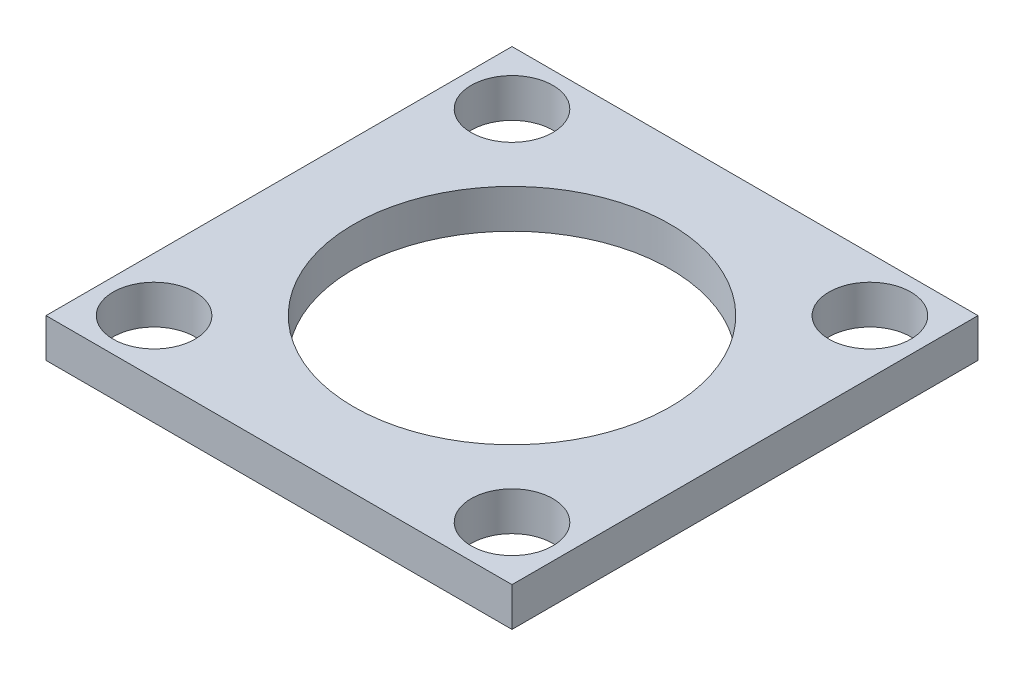
SolidWorks part; units mm, degrees
ref_plane "Plan de face" through (0, 0, 0) normal (0, 0, 1) x (1, 0, 0)
ref_plane "Plan de dessus" through (0, 0, 0) normal (0, 1, 0) x (1, 0, 0)
ref_plane "Plan de droite" through (0, 0, 0) normal (1, 0, 0) x (0, 0, -1)
sketch "Esquisse1" plane through (0, 0, 0) normal (0, 1, 0) x (1, 0, 0)
  line L1 (0, 0) -> (6, 0)
  line L2 (0, 0) -> (0, 6)
  line L3 (0, 6) -> (6, 6)
  line L4 (6, 0) -> (6, 6)
  dimension "D1" = 6
  dimension "D2" = 6
extrude "Extrusion1" add sketch "Esquisse1" along normal blind 0.5
sketch "Esquisse2" plane through (0, 0.5, 0) normal (0, 1, 0) x (-1, 0, 0)
  circle A0 centre (-3, -3) radius 2.0371
extrude "Enlèv. mat.-Extru.1" cut sketch "Esquisse2" against normal through all
sketch "Esquisse3" plane through (0, 0.5, 0) normal (0, 1, 0) x (-1, 0, 0)
  line L0 (0, -6) -> (-6, 0) construction
  line L1 (-6, -6) -> (0, 0) construction
  line L2 (-0.6959, -5.3041) -> (-5.3041, -5.3041) construction
  line L3 (-5.3041, -5.3041) -> (-5.3041, -0.6959) construction
  line L4 (-5.3041, -0.6959) -> (-0.6959, -0.6959) construction
  line L5 (-0.6959, -0.6959) -> (-0.6959, -5.3041) construction
  circle A0 centre (-0.6959, -5.3041) radius 0.5266
  circle A1 centre (-5.3041, -5.3041) radius 0.5266
  circle A2 centre (-5.3041, -0.6959) radius 0.5266
  circle A3 centre (-0.6959, -0.6959) radius 0.5266
extrude "Enlèv. mat.-Extru.3" cut sketch "Esquisse3" against normal through all
